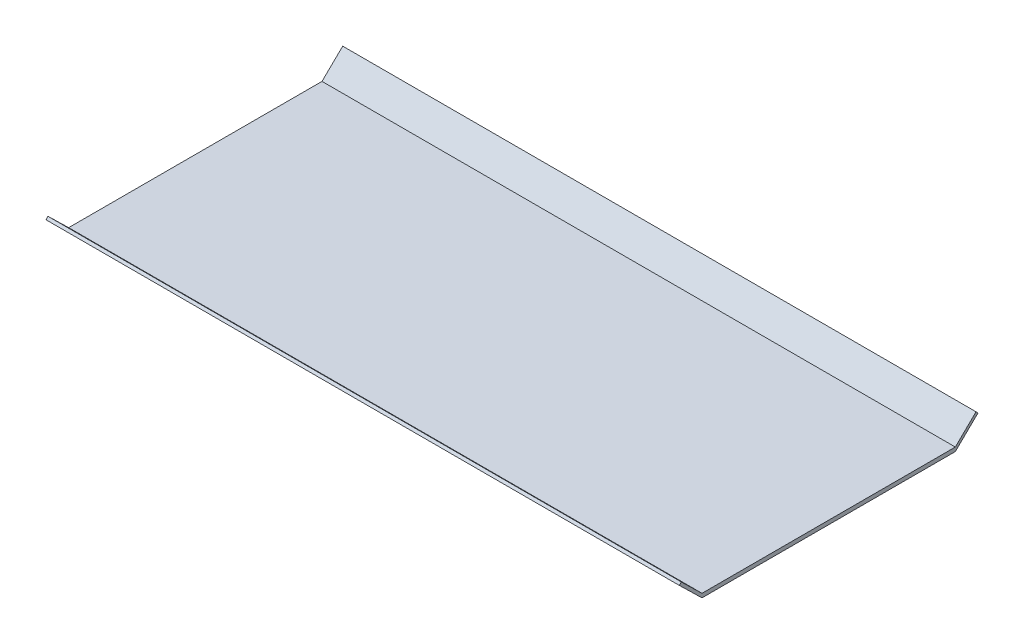
SolidWorks part; units mm, degrees
ref_plane "Front Plane" through (0, 0, 0) normal (0, 0, 1) x (1, 0, 0)
ref_plane "Top Plane" through (0, 0, 0) normal (0, 1, 0) x (1, 0, 0)
ref_plane "Right Plane" through (0, 0, 0) normal (1, 0, 0) x (0, 0, -1)
sketch "Sketch1" plane through (0, 0, 0) normal (0, 1, 0) x (1, 0, 0)
  line L1 (0, 0) -> (1016, 0)
  line L2 (0, 0) -> (0, 406.4)
  line L3 (0, 406.4) -> (1016, 406.4)
  line L4 (1016, 0) -> (1016, 406.4)
  dimension "D1" = 1016
  dimension "D2" = 406.4
extrude "Boss-Extrude1" add sketch "Sketch1" along normal blind 6.35
sketch "Sketch2" plane through (0, 0, 0) normal (1, 0, 0) x (0, 0, -1)
  line L0 (0, 0) -> (-36.3783, 35.4578)
  line L1 (-36.3783, 35.4578) -> (-33.2043, 38.7142)
  line L2 (-33.2043, 38.7142) -> (0, 6.35)
  line L3 (0, 6.35) -> (0, 0)
  line L4 (203.2, 6.35) -> (203.2, 124.0751) construction
  line L5 (406.4, 6.35) -> (0, 6.35) construction
  line L7 (406.4, 6.35) -> (406.4, 0)
  line L8 (439.6043, 38.7142) -> (406.4, 6.35)
  line L9 (442.7783, 35.4578) -> (439.6043, 38.7142)
  line L10 (406.4, 0) -> (442.7783, 35.4578)
  dimension "D1" = 50.8
extrude "Boss-Extrude2" add sketch "Sketch2" along direction (-1, 0, 0) on the side of the normal up to surface (1016 mm away)
